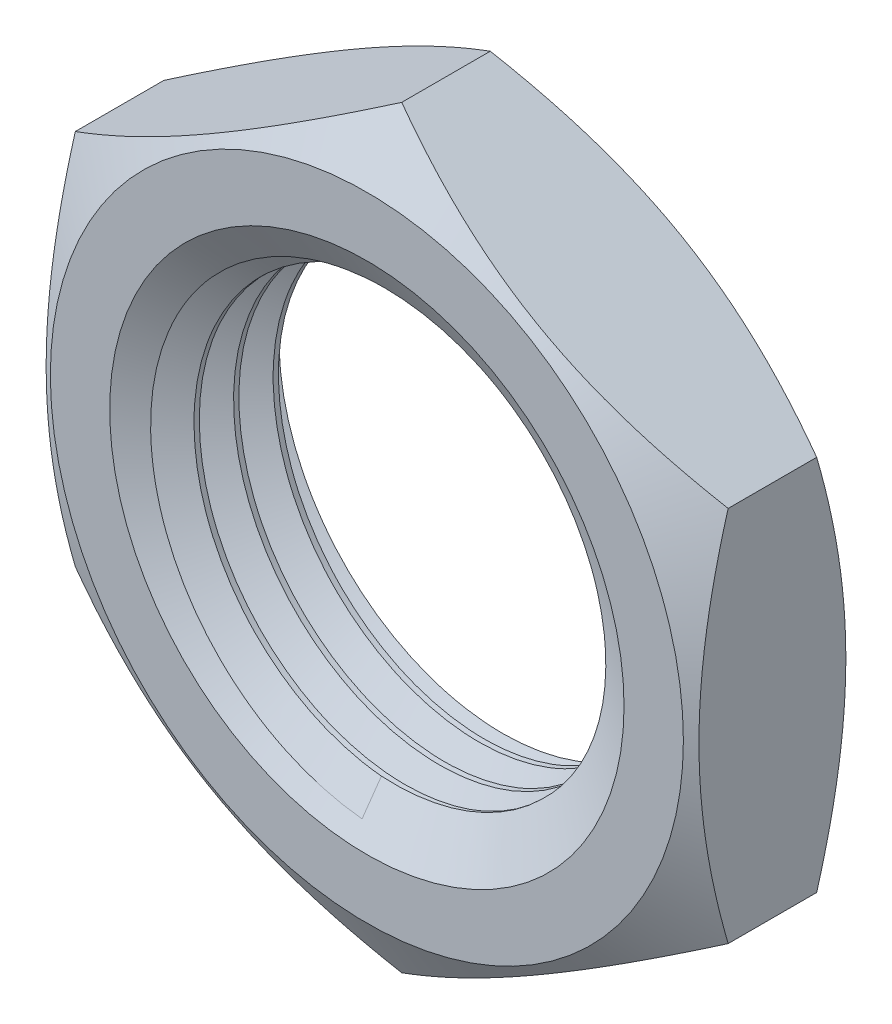
SolidWorks part; units mm, degrees
ref_plane "Спереди" through (0, 0, 0) normal (0, 0, 1) x (1, 0, 0)
ref_plane "Сверху" through (0, 0, 0) normal (0, 1, 0) x (1, 0, 0)
ref_plane "Справа" through (0, 0, 0) normal (1, 0, 0) x (0, 0, -1)
sketch "Эскиз1" plane through (0, 0, 0) normal (1, 0, 0) x (0, 0, -1)
  line L0 (0, 41.7471) -> (0, 0) construction
  line L1 (0, 0) -> (35.9696, 0) construction
  line L3 (0, 5.3) -> (4, 5.3)
  line L4 (0, 5.3) -> (0, 10.75)
  line L5 (0, 10.75) -> (4, 10.75)
  line L6 (4, 5.3) -> (4, 10.75)
  dimension "D1" = 4
  dimension "D2" = 21.5
  dimension "D3" = 10.6
revolve "Повернуть1" add sketch "Эскиз1" angle 360 about L1
sketch "Эскиз2" plane through (0, 0, 0) normal (0, 0, 1) x (1, 0, 0)
  line L1 (8.25, -4.7631) -> (8.25, 4.7631)
  line L2 (8.25, 4.7631) -> (0, 9.5263)
  line L3 (0, 9.5263) -> (-8.25, 4.7631)
  line L4 (-8.25, 4.7631) -> (-8.25, -4.7631)
  line L5 (-8.25, -4.7631) -> (0, -9.5263)
  line L6 (0, -9.5263) -> (8.25, -4.7631)
  circle A0 centre (0, 0) radius 8.25 construction
  circle A1 centre (0, 0) radius 11
  dimension "D1" = 22
  dimension "D2" = 16.5
extrude "Вырез-Вытянуть1" cut sketch "Эскиз2" against normal through all
sketch "Эскиз3" plane through (0, 0, 0) normal (1, 0, 0) x (0, 0, -1)
  line L0 (0, 0) -> (4, 0) construction
  line L1 (4, -5.3) -> (4, 5.3) construction
  line L2 (4, 0) -> (4, 6.5) construction
  line L3 (4, 4.7631) -> (4, 9.5263) construction
  line L4 (4, 6.5) -> (0, 6.5) construction
  line L5 (0, 4.7631) -> (0, 9.5263) construction
  line L6 (0, 6.5) -> (0, 8) construction
  line L7 (0, 8) -> (4, 8) construction
  line L8 (2, 3.0359) -> (4, 6.5)
  line L9 (4, 6.5) -> (4, 8)
  line L10 (4, 8) -> (2.8453, 10)
  line L11 (2.8453, 10) -> (1.1547, 10)
  line L12 (1.1547, 10) -> (0, 8)
  line L13 (0, 8) -> (0, 6.5)
  line L14 (0, 6.5) -> (2, 3.0359)
  line L16 (5, 11) -> (-1, 11)
  line L17 (5, 11) -> (5, 2.0359)
  line L18 (5, 2.0359) -> (-1, 2.0359)
  line L19 (-1, 11) -> (-1, 2.0359)
  dimension "D1" = 8
  dimension "D2" = 6.5
  dimension "D3" = 60
  dimension "D4" = 60
  dimension "D5" = 10
  dimension "D6" = 1
  dimension "D7" = 1
  dimension "D8" = 1
  dimension "D9" = 1
revolve "Вырез-Повернуть1" cut sketch "Эскиз3" angle 360 about L0
sketch "Эскиз4" plane through (0, 0, -4) normal (0, 0, -1) x (-1, 0, 0)
  circle A0 centre (0, 0) radius 6.05
  dimension "D1" = 12.1
curve "Спираль1" pitch 1 height 10 turns 10
ref_plane "Плоскость1" through (-6.05, 0, -4) normal (0, -0.9997, 0.0263) x (-1, 0, 0)
sketch "Эскиз5" plane through (-6.05, 0, -4) normal (0, -0.9997, 0.0263) x (-1, 0, 0)
  line L0 (-0.8617, 0.9975) -> (0, 0.5)
  line L1 (0, 0.5) -> (-0.8617, 0.0025)
  line L2 (-0.8617, 0.0025) -> (-0.8617, 0.9975)
  dimension "D1" = 0.995
  dimension "D2" = 60
sweep "Вырез-По траектории1" cut profiles "Эскиз5" path "Спираль1"
